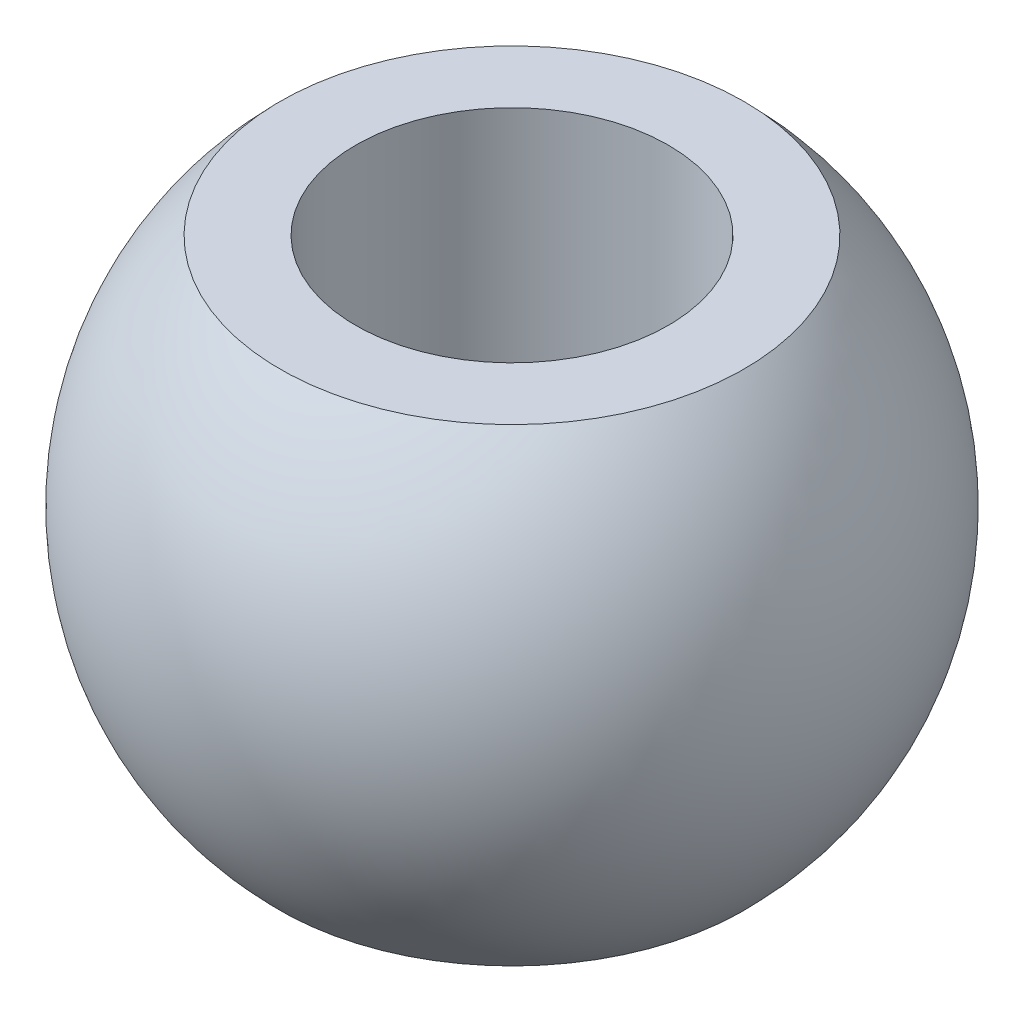
SolidWorks part; units mm, degrees
material "1.0545 (S355N)"
ref_plane "Płaszczyzna przednia" through (0, 0, 0) normal (0, 0, 1) x (1, 0, 0)
ref_plane "Płaszczyzna górna" through (0, 0, 0) normal (0, 1, 0) x (1, 0, 0)
ref_plane "Płaszczyzna prawa" through (0, 0, 0) normal (1, 0, 0) x (0, 0, -1)
sketch "Szkic1" plane through (0, 0, 0) normal (0, 0, 1) x (1, 0, 0)
  line L0 (0, -11.1) -> (0, 11.1) construction
  line L1 (3, -4.5) -> (3, 4.5)
  line L2 (3, 4.5) -> (4.4518, 4.5)
  line L3 (3, -4.5) -> (4.4518, -4.5)
  arc A0 (4.4518, -4.5) -> (4.4518, 4.5) centre (0, 0) ccw
  point P6 (3, 0)
  dimension "d3" = 12.66
  dimension "d1" = 3
  dimension "b1" = 9
revolve "Obrót1" add sketch "Szkic1" angle 360 about L0
